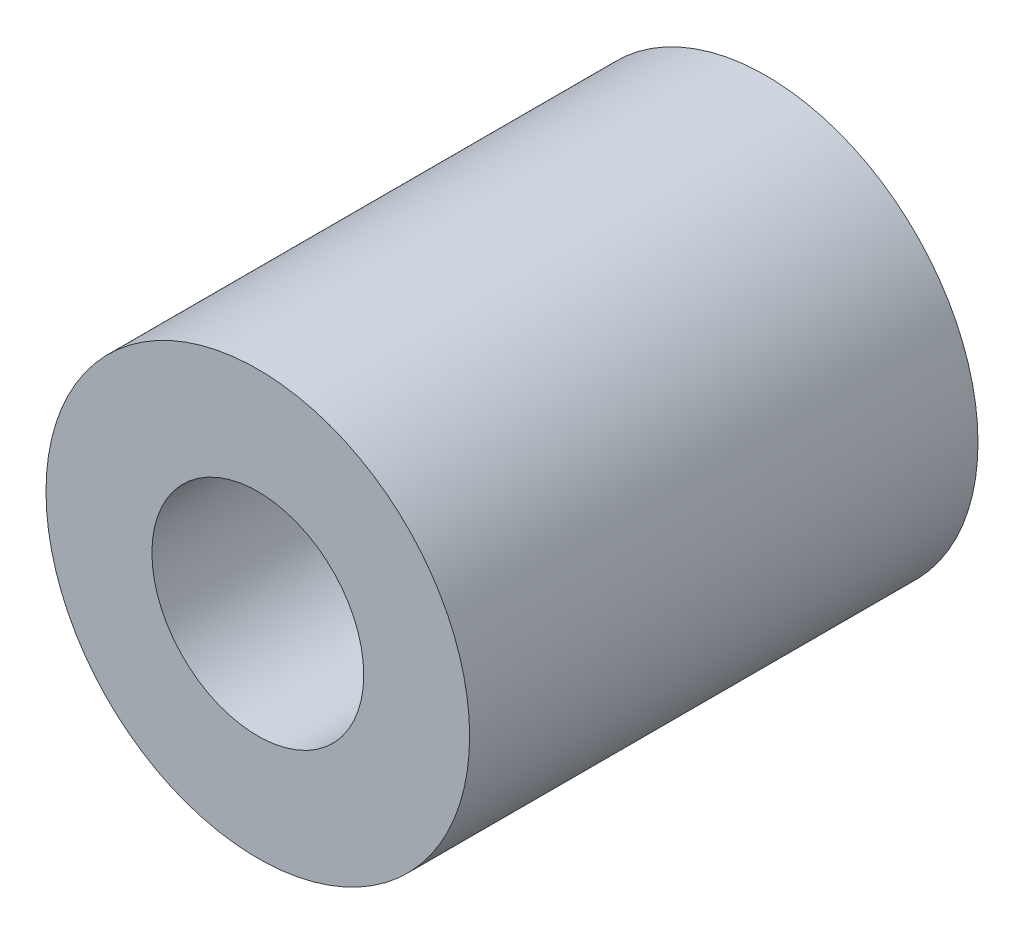
SolidWorks part; units mm, degrees
ref_plane "Front Plane" through (0, 0, 0) normal (0, 0, 1) x (1, 0, 0)
ref_plane "Top Plane" through (0, 0, 0) normal (0, 1, 0) x (1, 0, 0)
ref_plane "Right Plane" through (0, 0, 0) normal (1, 0, 0) x (0, 0, -1)
sketch "Sketch1" plane through (0, 0, 0) normal (0, 0, 1) x (1, 0, 0)
  circle A0 centre (0, 0) radius 5
  dimension "D1" = 10
extrude "Boss-Extrude1" add sketch "Sketch1" along normal blind 12
hole_wizard "Ø5.0mm Dowel Hole1" positions "Sketch2" profile "Sketch3" hole size "Ø5.0" standard "ANSI Metric" end condition up to next
sketch "Sketch2" plane through (0, 0, 12) normal (0, 0, 1) x (1, 0, 0)
  point P0 (0, 0)
sketch "Sketch3" plane through (0, 0, 12) normal (1, 0, 0) x (0, -1, 0)
  line L0 (0, 0) -> (0, 12)
  line L1 (0, 12) -> (2.5, 12)
  line L2 (2.5, 12) -> (2.5, 0)
  line L5 (2.5, 0) -> (0, 0)
  line L11 (0, -6.35) -> (0, 107.95) construction
  dimension "Thru Hole Dia." = 5
  dimension "Thru Hole Depth" = 12
equation "\"Length\"=12"
equation "\"D1@Boss-Extrude1\"=\"Length\""
